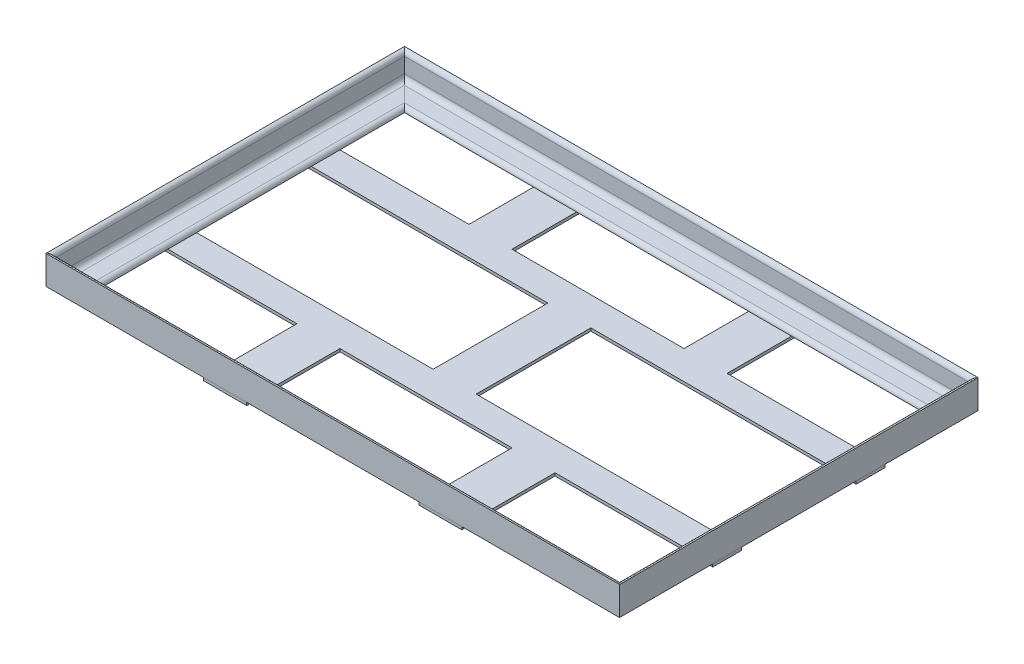
SolidWorks part; units mm, degrees
ref_plane "Alzado" through (0, 0, 0) normal (0, 0, 1) x (1, 0, 0)
ref_plane "Planta" through (0, 0, 0) normal (0, 1, 0) x (1, 0, 0)
ref_plane "Vista lateral" through (0, 0, 0) normal (1, 0, 0) x (0, 0, -1)
sketch "Croquis1" plane through (0, 0, 0) normal (0, 1, 0) x (1, 0, 0)
  line L0 (0, -125) -> (0, 125)
  line L1 (-200, -125) -> (200, -125)
  line L2 (-200, -125) -> (-200, 125)
  line L3 (-200, 125) -> (200, 125)
  line L4 (200, -125) -> (200, 125)
  line L5 (-200, -125) -> (200, 125) construction
  line L6 (-200, 125) -> (200, -125) construction
  line L7 (-200, 50) -> (200, 50)
  line L8 (-200, -50) -> (200, -50)
  line L9 (-75, 125) -> (-75, 50)
  line L10 (-75, -50) -> (-75, -125)
  line L11 (75, 125) -> (75, 50)
  line L12 (75, -50) -> (75, -125)
  line L13 (-200, 0) -> (200, 0) construction
  point P0 (0, 0)
  point P9 (0, 0)
  point P23 (-75, -87.5)
  dimension "D1" = 250
  dimension "D2" = 400
  dimension "D3" = 50
  dimension "D4" = 50
  dimension "D5" = 150
  dimension "D6" = 75
other "Hierro angular 20 X 20 X 3(1)"
ref_plane "Plano1" through (-200, 0, 125) normal (1, 0, 0) x (0, 0, -1)
sketch "Sketch1" plane through (-200, 0, 125) normal (1, 0, 0) x (0, 0, -1)
  line L0 (0, 0) -> (0, 20)
  line L1 (0, 10) -> (3, 10) construction
  line L2 (3, 17) -> (3, 6.5)
  line L3 (6.5, 3) -> (17, 3)
  line L4 (10, 3) -> (10, 0) construction
  line L5 (20, 0) -> (0, 0)
  arc A0 (20, 0) -> (17, 3) centre (17, 0) ccw
  arc A1 (0, 20) -> (3, 17) centre (0, 17) cw
  arc A2 (6.5, 3) -> (3, 6.5) centre (6.5, 6.5) cw
  point P10 (10, 0)
  point P14 (0, 10)
  point P15 (3, 10)
  point P16 (10, 3)
  point P17 (3, 20)
  point P18 (20, 3)
  point P21 (0, 0)
  dimension "D2" = 3
  dimension "D3" = 20
  dimension "Radius_1" = 3.5
  dimension "D1" = 3
sketch "Croquis3" plane through (0, 0, 0) normal (0, -1, 0) x (1, 0, 0)
  line L40 (-15, 125) -> (-15, -125)
  line L41 (-15, 125) -> (-15, -125) construction
  line L42 (15, 125) -> (15, -125)
  line L43 (15, 125) -> (15, -125) construction
  line L48 (-200, -60) -> (200, -60)
  line L49 (-200, -60) -> (200, -60) construction
  line L50 (-200, -40) -> (200, -40)
  line L51 (-200, -40) -> (200, -40) construction
  line L53 (-200, 40) -> (200, 40)
  line L54 (-200, 40) -> (200, 40) construction
  line L55 (-200, 60) -> (200, 60)
  line L56 (-200, 60) -> (200, 60) construction
  line L64 (-60, -125) -> (-60, -50)
  line L65 (-60, -125) -> (-60, -50) construction
  line L66 (-90, -125) -> (-90, -50)
  line L67 (-90, -125) -> (-90, -50) construction
  line L69 (-60, 50) -> (-60, 125)
  line L70 (-60, 50) -> (-60, 125) construction
  line L71 (-90, 50) -> (-90, 125)
  line L72 (-90, 50) -> (-90, 125) construction
  line L74 (90, 50) -> (90, 125)
  line L75 (90, 50) -> (90, 125) construction
  line L76 (60, 50) -> (60, 125)
  line L77 (60, 50) -> (60, 125) construction
  line L78 (-200, -60) -> (-90, -60)
  line L79 (90, -125) -> (90, -50)
  line L80 (90, -125) -> (90, -50) construction
  line L81 (60, -125) -> (60, -50)
  line L82 (60, -125) -> (60, -50) construction
  line L83 (-90, -60) -> (-90, -125)
  line L84 (-90, -125) -> (-60, -125)
  line L85 (-60, -125) -> (-60, -60)
  line L86 (-60, -60) -> (-15, -60)
  line L87 (-15, -60) -> (15, -60)
  line L88 (-15, 60) -> (15, 60)
  line L90 (15, -60) -> (60, -60)
  line L91 (60, -60) -> (60, -125)
  line L92 (60, -125) -> (90, -125)
  line L93 (90, -125) -> (90, -60)
  line L94 (90, -60) -> (200, -60)
  line L95 (200, -60) -> (200, -40)
  line L96 (200, -40) -> (15, -40)
  line L97 (15, -40) -> (15, 40)
  line L98 (15, 40) -> (200, 40)
  line L99 (200, 40) -> (200, 60)
  line L100 (200, 60) -> (90, 60)
  line L101 (90, 60) -> (90, 125)
  line L102 (90, 125) -> (60, 125)
  line L103 (60, 125) -> (60, 60)
  line L104 (60, 60) -> (15, 60)
  line L108 (-15, 60) -> (-60, 60)
  line L109 (-60, 60) -> (-60, 125)
  line L110 (-60, 125) -> (-90, 125)
  line L111 (-90, 125) -> (-90, 60)
  line L112 (-90, 60) -> (-200, 60)
  line L113 (-200, 60) -> (-200, 40)
  line L114 (-200, 40) -> (-15, 40)
  line L115 (-15, 40) -> (-15, -40)
  line L116 (-15, -40) -> (-200, -40)
  line L117 (-200, -40) -> (-200, -60)
  dimension "D1" = 15
  dimension "D2" = 15
  dimension "D3" = 10
  dimension "D4" = 10
  dimension "D5" = 10
  dimension "D6" = 10
  dimension "D7" = 15
  dimension "D8" = 15
  dimension "D9" = 15
  dimension "D10" = 15
  dimension "D11" = 15
  dimension "D12" = 15
  dimension "D13" = 15
  dimension "D14" = 15
extrude "Saliente-Extruir1" add sketch "Croquis3" along normal blind 2 separate body
